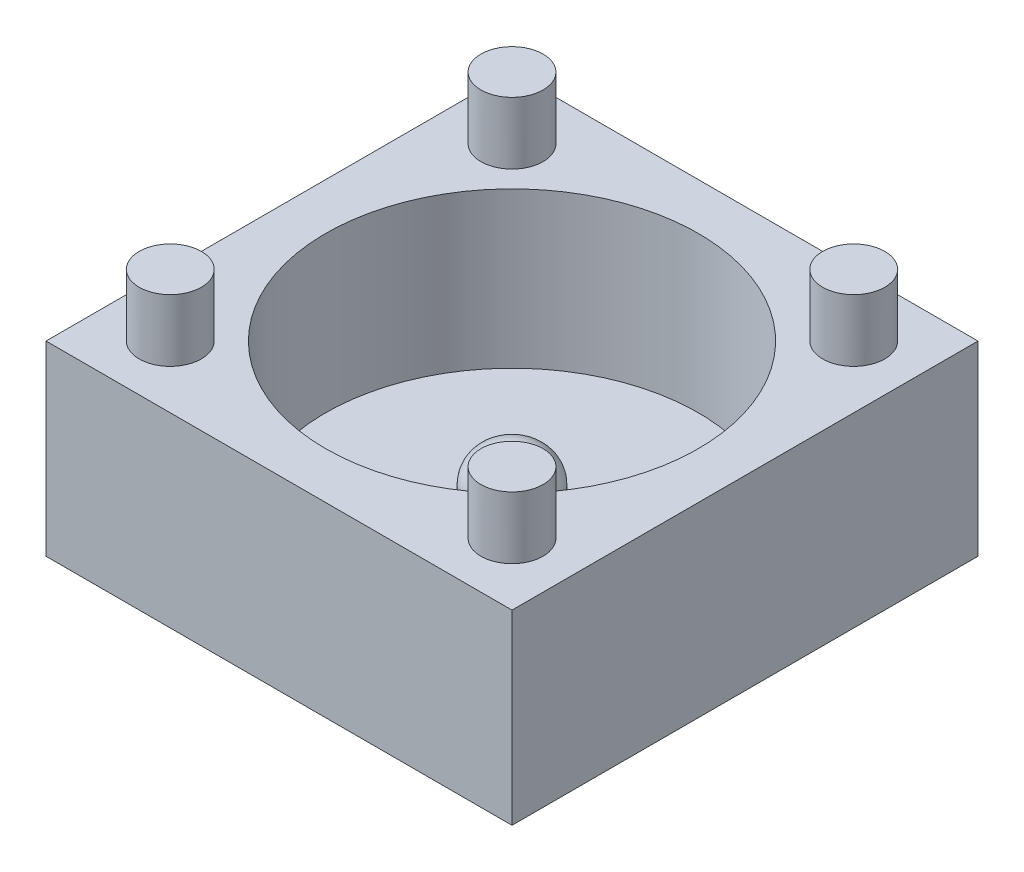
SolidWorks part; units mm, degrees
ref_plane "Front Plane" through (0, 0, 0) normal (0, 0, 1) x (1, 0, 0)
ref_plane "Top Plane" through (0, 0, 0) normal (0, 1, 0) x (1, 0, 0)
ref_plane "Right Plane" through (0, 0, 0) normal (1, 0, 0) x (0, 0, -1)
sketch "Sketch1" plane through (0, 0, 0) normal (0, 1, 0) x (1, 0, 0)
  line L1 (-7.5, -7.5) -> (7.5, -7.5)
  line L2 (-7.5, -7.5) -> (-7.5, 7.5)
  line L3 (-7.5, 7.5) -> (7.5, 7.5)
  line L4 (7.5, -7.5) -> (7.5, 7.5)
  line L5 (-7.5, -7.5) -> (7.5, 7.5) construction
  line L6 (-7.5, 7.5) -> (7.5, -7.5) construction
  point P0 (0, 0)
  dimension "D1" = 15
  dimension "D2" = 15
extrude "Boss-Extrude1" add sketch "Sketch1" along normal blind 6
sketch "Sketch2" plane through (0, 6, 0) normal (0, 1, 0) x (1, 0, 0)
  circle A0 centre (0, 0) radius 6
  dimension "D1" = 12
extrude "Cut-Extrude1" cut sketch "Sketch2" against normal blind 5
sketch "Sketch3" plane through (0, 1, 0) normal (0, 1, 0) x (1, 0, 0)
  circle A0 centre (0, 0) radius 1.25
  dimension "D1" = 2.5
extrude "Boss-Extrude2" add sketch "Sketch3" along normal blind 2
fillet "Fillet1" radius 1 1 edges at (0, 3, 1.25)
sketch "Sketch4" plane through (0, 6, 0) normal (0, 1, 0) x (1, 0, 0)
  line L0 (7.5, 7.5) -> (-7.5, 7.5) construction
  line L1 (-7.5, 7.5) -> (-7.5, -7.5) construction
  line L2 (-7.5, -7.5) -> (7.5, -7.5) construction
  line L3 (7.5, -7.5) -> (7.5, 7.5) construction
  circle A0 centre (-5.5, 5.5) radius 1
  circle A1 centre (5.5, 5.5) radius 1
  circle A2 centre (-5.5, -5.5) radius 1
  circle A3 centre (5.5, -5.5) radius 1
  dimension "D1" = 2
  dimension "D4" = 2
  dimension "D7" = 2
  dimension "D10" = 2
  dimension "D2" = 2
  dimension "D3" = 2
  dimension "D5" = 2
  dimension "D6" = 2
  dimension "D8" = 2
  dimension "D9" = 2
  dimension "D11" = 2
  dimension "D12" = 2
extrude "Boss-Extrude3" add sketch "Sketch4" along normal blind 2
